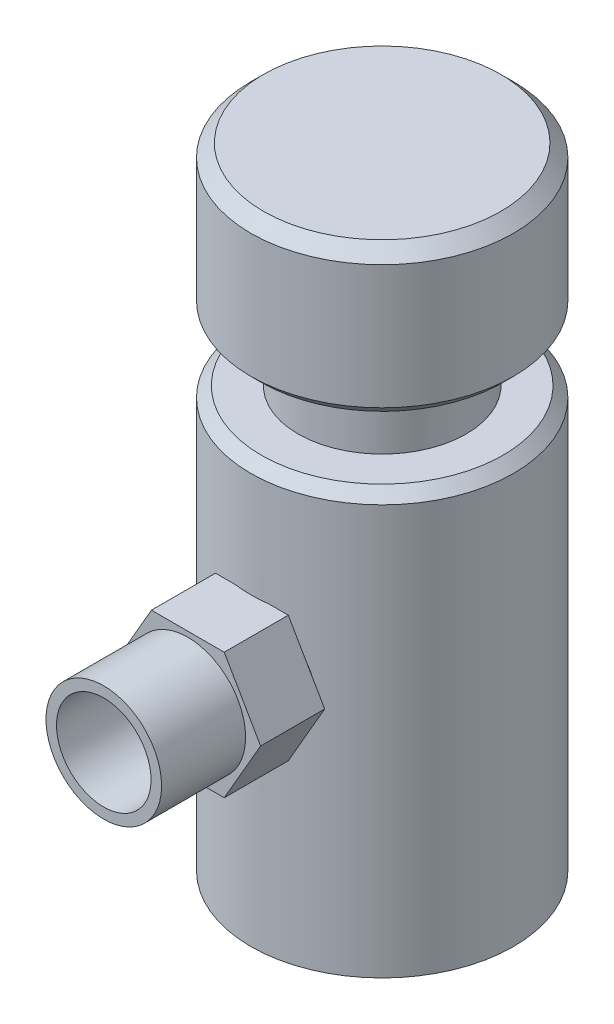
SolidWorks part; units mm, degrees
material "7075-T6 (SN)"
ref_plane "Front Plane" through (0, 0, 0) normal (0, 0, 1) x (1, 0, 0)
ref_plane "Top Plane" through (0, 0, 0) normal (0, 1, 0) x (1, 0, 0)
ref_plane "Right Plane" through (0, 0, 0) normal (1, 0, 0) x (0, 0, -1)
sketch "Sketch1" plane through (0, 0, 0) normal (0, 0, 1) x (1, 0, 0)
  line L0 (0, 17.6751) -> (0, -20.8509) construction
  line L1 (0, -44.7747) -> (12.5, -44.7747)
  line L2 (12.5, -44.7747) -> (12.5, -5.7747)
  line L5 (8, -4.7747) -> (8, 1.2253)
  line L6 (8, 1.2253) -> (11.5, 1.2253)
  line L7 (11.5, 1.2253) -> (12.5, 2.2253)
  line L8 (12.5, 2.2253) -> (12.5, 14.0202)
  line L9 (12.5, 14.0202) -> (11.2949, 15.2253)
  line L10 (11.2949, 15.2253) -> (0, 15.2253)
  line L11 (0, 15.2253) -> (0, -44.7747)
  line L12 (12.5, -5.7747) -> (11.5, -4.7747)
  line L13 (11.5, -4.7747) -> (8, -4.7747)
  dimension "D1" = 12.5
  dimension "D2" = 12.5
  dimension "D3" = 6
  dimension "D4" = 60
  dimension "D5" = 45
  dimension "D6" = 225
  dimension "D7" = 40
  dimension "D8" = 1
  dimension "D9" = 8
  dimension "D10" = 3.5
revolve "Revolve1" add sketch "Sketch1" angle 360 about L0
hole_wizard "M20x2.0 Tapped Hole1" positions "Sketch4" profile "Sketch3" tap size "M20x2.0" standard "ANSI Metric"
sketch "Sketch4" plane through (0, -44.7747, 0) normal (0, -1, 0) x (-1, 0, 0)
  point P0 (0, 0)
sketch "Sketch3" plane through (0, -44.7747, 0) normal (1, 0, 0) x (0, 0, -1)
  line L0 (0, 0) -> (0, 21.4077)
  line L1 (0, 21.4077) -> (9, 16)
  line L2 (9, 16) -> (9, 0)
  line L5 (9, 0) -> (0, 0)
  line L10 (0, 21.4077) -> (-9, 16) construction
  line L11 (0, -6.35) -> (0, 107.95) construction
  dimension "Tap Drill Dia." = 18
  dimension "Tap Drill Depth" = 16
  dimension "Drill Angle" = 118
cosmetic thread "Hole Thread1" parameters "D1"=14, "D2"=20
sketch "Sketch5" plane through (0, 0, 0) normal (0, 0, 1) x (1, 0, 0)
  line L0 (0, 24.2029) -> (0, -55.0809) construction
  line L1 (-32.0142, -21.7747) -> (38.5159, -21.7747) construction
  line L2 (-12.5, -44.7747) -> (12.5, -44.7747) construction
  circle A0 centre (0, -21.7747) radius 5
  dimension "D2" = 10
  dimension "D1" = 23
extrude "Cut-Extrude1" cut sketch "Sketch5" against normal blind 10 from offset 12.5
ref_plane "Plane1" through (0, 0, 12.5) normal (0, 0, 1) x (1, 0, 0)
sketch "Sketch6" plane through (0, 0, 12.5) normal (0, 0, 1) x (1, 0, 0)
  circle A0 centre (0, -21.7747) radius 5
extrude "Boss-Extrude1" add sketch "Sketch6" against normal blind 2
sketch "Sketch7" plane through (0, 0, 12.5) normal (0, 0, 1) x (1, 0, 0)
  line L1 (6.9282, -21.7747) -> (3.4641, -15.7747)
  line L2 (3.4641, -15.7747) -> (-3.4641, -15.7747)
  line L3 (-3.4641, -15.7747) -> (-6.9282, -21.7747)
  line L4 (-6.9282, -21.7747) -> (-3.4641, -27.7747)
  line L5 (-3.4641, -27.7747) -> (3.4641, -27.7747)
  line L6 (3.4641, -27.7747) -> (6.9282, -21.7747)
  circle A0 centre (0, -21.7747) radius 6 construction
  arc A1 (0, -16.7747) -> (0, -26.7747) centre (0, -21.7747) ccw construction
  dimension "D1" = 1
extrude "Boss-Extrude2" add sketch "Sketch7" along normal blind 6 and the other way blind 0.1 separate body
sketch "Sketch8" plane through (0, 0, 18.5) normal (0, 0, 1) x (1, 0, 0)
  circle A0 centre (0, -21.7747) radius 5.5
  dimension "D1" = 11
extrude "Boss-Extrude3" add sketch "Sketch8" along normal blind 8
sketch "Sketch9" plane through (0, 0, 26.5) normal (0, 0, 1) x (1, 0, 0)
  circle A0 centre (0, -21.7747) radius 4.5
  circle A1 centre (0, -21.7747) radius 5.5 construction
  dimension "D1" = 1
extrude "Cut-Extrude2" cut sketch "Sketch9" against normal blind 25
